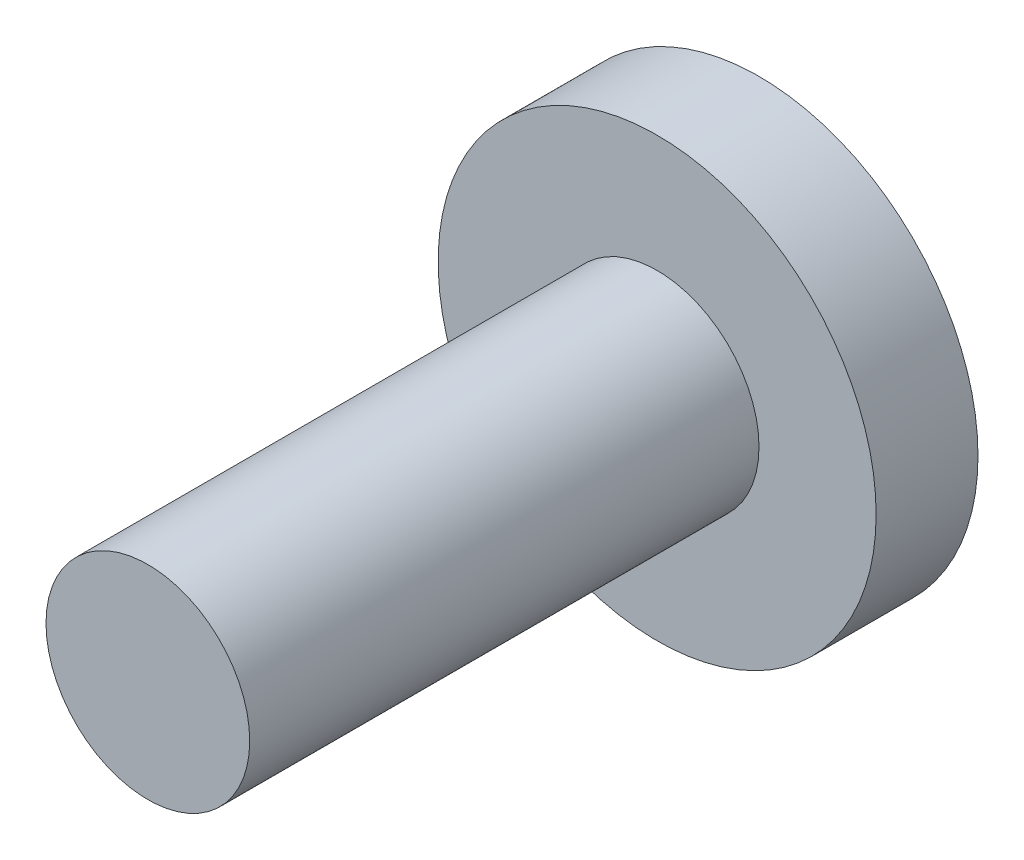
SolidWorks part; units mm, degrees
ref_plane "Alzado" through (0, 0, 0) normal (0, 0, 1) x (1, 0, 0)
ref_plane "Planta" through (0, 0, 0) normal (0, 1, 0) x (1, 0, 0)
ref_plane "Vista lateral" through (0, 0, 0) normal (1, 0, 0) x (0, 0, -1)
sketch "Model" plane through (0, 0, 0) normal (0, 0, 1) x (1, 0, 0)
  circle A1 centre (33.2, 15.9) radius 2.15
sketch "Croquis2" plane through (0, 0, 0) normal (0, 0, 1) x (1, 0, 0)
  circle A1 centre (33.2, 15.9) radius 1
extrude "Saliente-Extruir1" add sketch "Model" along normal blind 1
extrude "Saliente-Extruir2" add sketch "Croquis2" along normal blind 6
